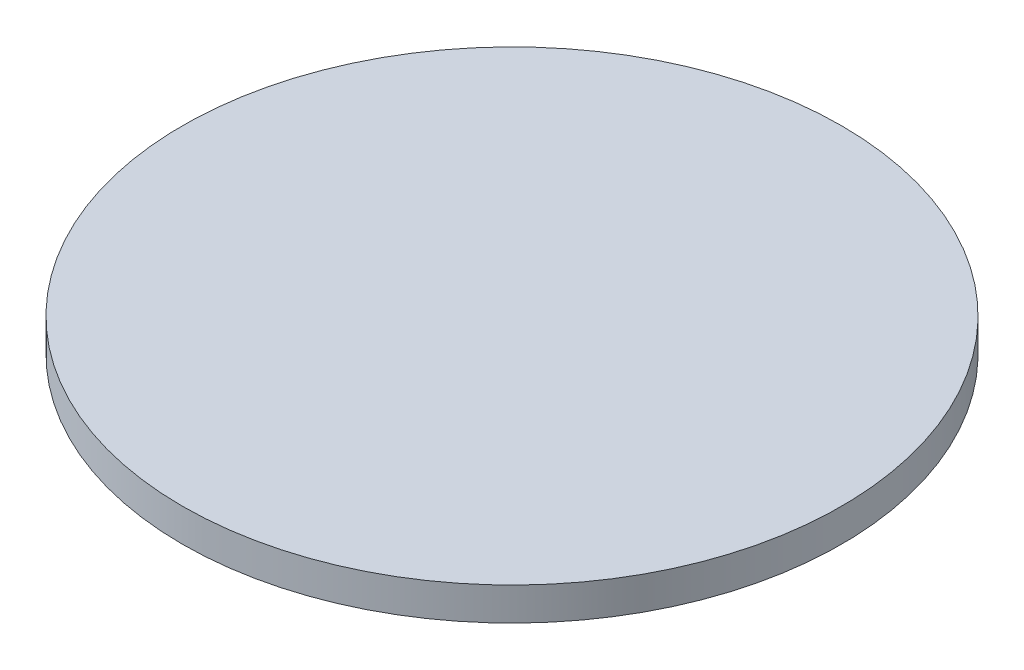
SolidWorks part; units mm, degrees
ref_plane "Front Plane" through (0, 0, 0) normal (0, 0, 1) x (1, 0, 0)
ref_plane "Top Plane" through (0, 0, 0) normal (0, 1, 0) x (1, 0, 0)
ref_plane "Right Plane" through (0, 0, 0) normal (1, 0, 0) x (0, 0, -1)
sketch "Sketch1" plane through (0, 0, 0) normal (0, 1, 0) x (1, 0, 0)
  circle A0 centre (0, 0) radius 50
  point P2 (0, 0)
  point P3 (0, 0)
  dimension "D1" = 100
extrude "Boss-Extrude1" add sketch "Sketch1" along normal blind 5
sketch "Sketch2" plane through (0, 0, 0) normal (0, 1, 0) x (1, 0, 0)
  circle A0 centre (0, 0) radius 20
  point P2 (0, 0)
  point P3 (0, 0)
  dimension "D1" = 40
curve "Helix/Spiral1"
sketch "Sketch4" plane through (0, 0, 0) normal (1, 0, 0) x (0, 0, -1)
  circle A0 centre (-20, 0) radius 1
  point P2 (-16.0185, -0.3046)
  point P3 (-6.7393, 0.0782)
  point P4 (0.9647, 28.0814)
  point P5 (0, 0)
  point P6 (0, 0)
  point P7 (0, 0)
  point P8 (0, 0)
  dimension "D1" = 2
